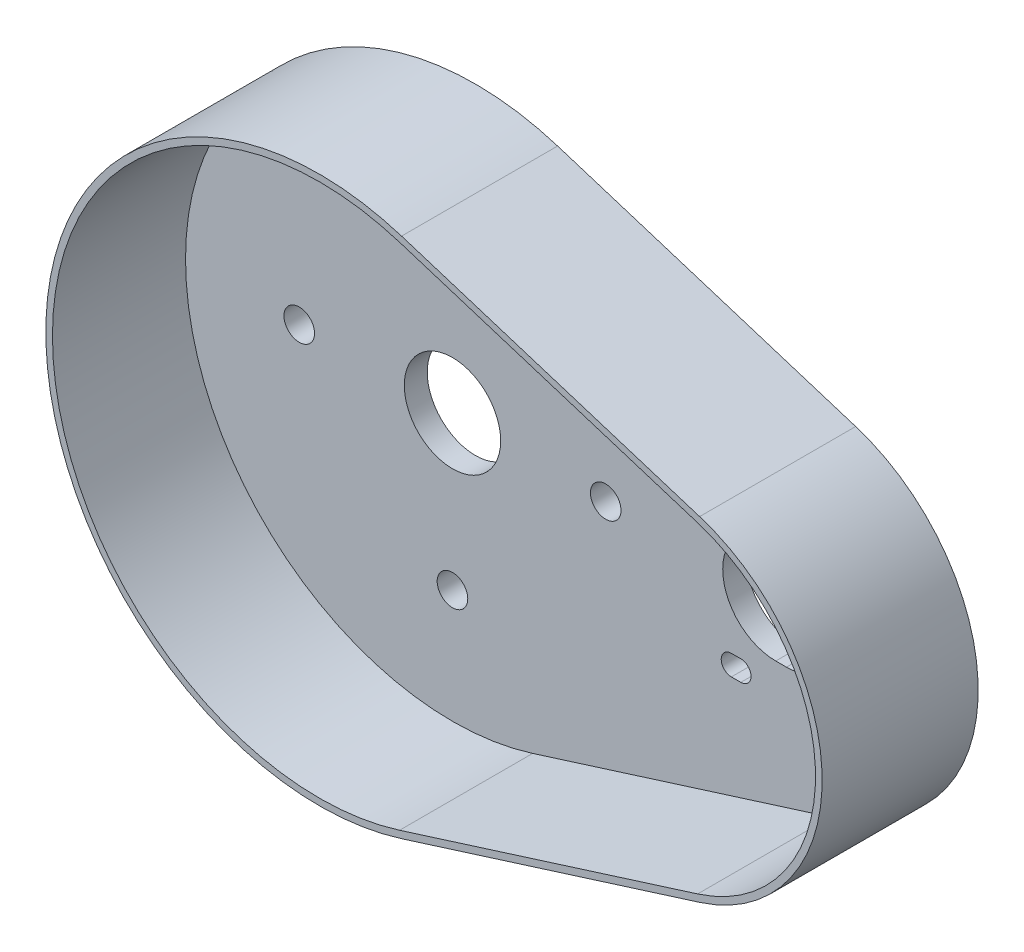
SolidWorks part; units mm, degrees
ref_plane "Front Plane" through (0, 0, 0) normal (0, 0, 1) x (1, 0, 0)
ref_plane "Top Plane" through (0, 0, 0) normal (0, 1, 0) x (1, 0, 0)
ref_plane "Right Plane" through (0, 0, 0) normal (1, 0, 0) x (0, 0, -1)
sketch "Sketch1" plane through (0, 0, 0) normal (0, 0, 1) x (1, 0, 0)
  line L0 (-9.45, 0) -> (-53.65, 0) construction
  line L1 (-9.45, 0) -> (33.05, 0) construction
  line L2 (63.4, 0) -> (65.5, 0) construction
  line L3 (63.4, 10.4) -> (65.5, 10.4)
  line L4 (63.4, -10.4) -> (65.5, -10.4)
  line L5 (85.7511, 15.45) -> (87.6011, 15.45) construction
  line L6 (85.7511, 17.45) -> (87.6011, 17.45)
  line L7 (85.7511, 13.45) -> (87.6011, 13.45)
  line L8 (54.7011, 15.45) -> (56.5511, 15.45) construction
  line L9 (54.7011, 17.45) -> (56.5511, 17.45)
  line L10 (54.7011, 13.45) -> (56.5511, 13.45)
  line L11 (85.7511, -15.45) -> (87.6011, -15.45) construction
  line L12 (85.7511, -17.45) -> (87.6011, -17.45)
  line L13 (85.7511, -13.45) -> (87.6011, -13.45)
  line L14 (54.7011, -15.45) -> (56.5511, -15.45) construction
  line L15 (54.7011, -17.45) -> (56.5511, -17.45)
  line L16 (54.7011, -13.45) -> (56.5511, -13.45)
  line L17 (83.7511, -15.45) -> (89.6011, -15.45) construction
  line L18 (16.1174, 51.1718) -> (74.5711, 32.7609)
  line L19 (16.1174, -51.1718) -> (74.5711, -32.7609)
  line L20 (53, 0) -> (75.9, 0) construction
  line L21 (98.6, 0) -> (98.6, 11.6645) construction
  line L22 (89.269, -16.5537) -> (92.8967, -18.9542) construction
  line L23 (89.269, -16.5537) -> (84.7224, -23.4247) construction
  line L24 (91.5062, -21.0555) -> (92.8967, -18.9542) construction
  line L25 (59.1853, -9.5077) -> (55.3058, -7.7879) construction
  line L26 (59.1853, -9.5077) -> (57.3616, -13.6216) construction
  line L27 (57.3616, -13.6216) -> (59.1913, -14.4327) construction
  circle A0 centre (0, 0) radius 53.65
  circle A1 centre (0, 0) radius 9.45
  circle A2 centre (0, 0) radius 30.05 construction
  circle A3 centre (0, 30.05) radius 3
  circle A4 centre (30.05, 0) radius 3
  circle A5 centre (0, -30.05) radius 3
  circle A6 centre (-30.05, 0) radius 3
  circle A7 centre (64.2526, 0) radius 34.3474
  arc A8 (63.4, 10.4) -> (63.4, -10.4) centre (63.4, 0) ccw
  arc A9 (65.5, -10.4) -> (65.5, 10.4) centre (65.5, 0) ccw
  arc A10 (85.7511, 17.45) -> (85.7511, 13.45) centre (85.7511, 15.45) ccw
  arc A11 (87.6011, 13.45) -> (87.6011, 17.45) centre (87.6011, 15.45) ccw
  arc A12 (54.7011, 17.45) -> (54.7011, 13.45) centre (54.7011, 15.45) ccw
  arc A13 (56.5511, 13.45) -> (56.5511, 17.45) centre (56.5511, 15.45) ccw
  arc A14 (85.7511, -17.45) -> (85.7511, -13.45) centre (85.7511, -15.45) cw
  arc A15 (87.6011, -13.45) -> (87.6011, -17.45) centre (87.6011, -15.45) cw
  arc A16 (54.7011, -17.45) -> (54.7011, -13.45) centre (54.7011, -15.45) cw
  arc A17 (56.5511, -13.45) -> (56.5511, -17.45) centre (56.5511, -15.45) cw
  point P18 (64.45, 0)
  point P25 (86.6761, 15.45)
  point P34 (55.6261, 15.45)
  point P41 (86.6761, -15.45)
  point P48 (55.6261, -15.45)
  point P58 (52.7011, -15.45)
  point P62 (9.45, 0)
  dimension "D1" = 18.9
  dimension "D2" = 6
  dimension "D5" = 4
  dimension "D9" = 20.8
  dimension "D12" = 22.7
  dimension "D3" = 44.2
  dimension "D4" = 42.5
  dimension "D6" = 34.9
  dimension "D7" = 5.85
  dimension "D8" = 36.9
  dimension "D10" = 22.9
  dimension "D11" = 43.55
  dimension "D13" = 152.25
  dimension "D14" = 4.35
  dimension "D15" = 4.5
extrude "Boss-Extrude1" add sketch "Sketch1" along normal blind 30.6 contours A7 A0 A4 A6 A5 A3 A1 | A8 A0 A7 A4 | A9 L4 A8 A0 A7 L3 A13 L10 A12 L9 A11 L7 A10 L6 L13 A15 L12 A14 L16 A17 L15 A16 | A7 L18 A0 | A7 A0 L19
sketch "Sketch2" plane through (0, 0, 30.6) normal (0, 0, 1) x (1, 0, 0)
  line L6 (74.1806, 31.5209) -> (15.7268, 49.9318)
  line L7 (15.7268, -49.9318) -> (74.1806, -31.5209)
  line L8 (74.1806, 31.5209) -> (15.7268, 49.9318)
  line L9 (15.7268, -49.9318) -> (74.1806, -31.5209)
  arc A8 (15.7268, 49.9318) -> (15.7268, -49.9318) centre (0, 0) ccw
  arc A9 (74.1806, -31.5209) -> (74.1806, 31.5209) centre (64.2526, 0) ccw
  arc A10 (15.7268, 49.9318) -> (15.7268, -49.9318) centre (0, 0) ccw
  arc A11 (74.1806, -31.5209) -> (74.1806, 31.5209) centre (64.2526, 0) ccw
  dimension "D1" = 1.3
extrude "Cut-Extrude1" cut sketch "Sketch2" against normal blind 26.1
